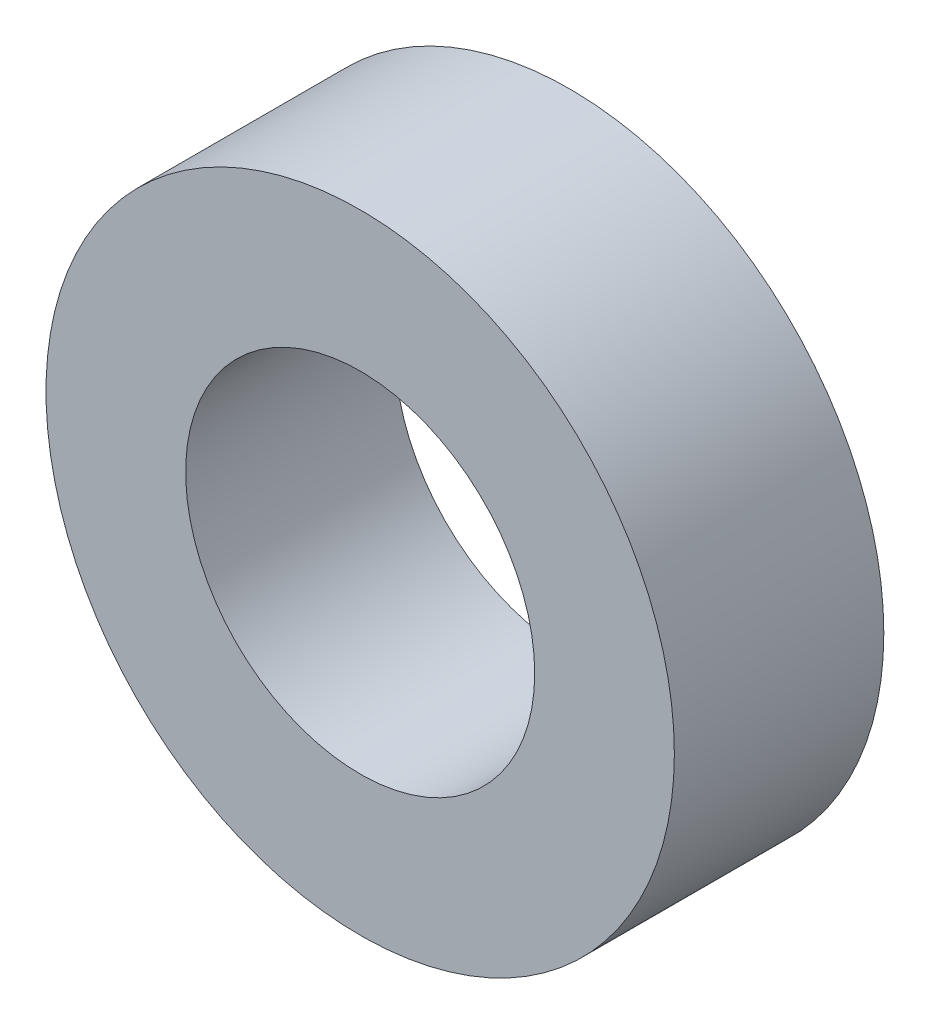
SolidWorks part; units mm, degrees
ref_plane "Alzado" through (0, 0, 0) normal (0, 0, 1) x (1, 0, 0)
ref_plane "Planta" through (0, 0, 0) normal (0, 1, 0) x (1, 0, 0)
ref_plane "Vista lateral" through (0, 0, 0) normal (1, 0, 0) x (0, 0, -1)
sketch "Croquis1" plane through (0, 0, 0) normal (0, 0, 1) x (1, 0, 0)
  circle A0 centre (0, 0) radius 2.5
  circle A1 centre (0, 0) radius 4.5
  dimension "D1" = 5
  dimension "D2" = 2
extrude "Saliente-Extruir1" add sketch "Croquis1" along normal blind 3
